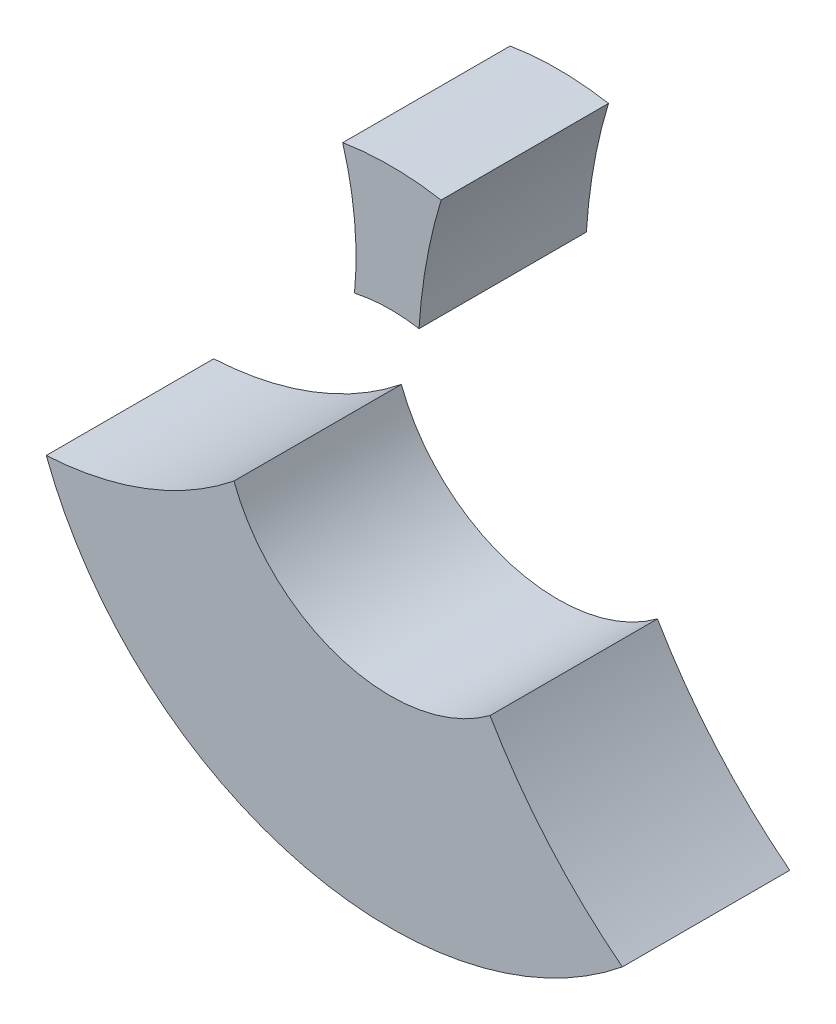
SolidWorks part; units mm, degrees
ref_plane "Front Plane" through (0, 0, 0) normal (0, 0, 1) x (1, 0, 0)
ref_plane "Top Plane" through (0, 0, 0) normal (0, 1, 0) x (1, 0, 0)
ref_plane "Right Plane" through (0, 0, 0) normal (1, 0, 0) x (0, 0, -1)
sketch "Sketch1" plane through (0, 0, 0) normal (0, 0, 1) x (1, 0, 0)
  circle A0 centre (0, 0) radius 6
  circle A1 centre (0, 0) radius 13.2
extrude "Boss-Extrude1" add sketch "Sketch1" along normal blind 6
sketch "Sketch2" plane through (0, 0, 6) normal (0, 0, 1) x (1, 0, 0)
  line L0 (0, 0) -> (0, 15.2) construction
  line L1 (-1.7101, 4.6985) -> (0, 0) construction
  line L2 (1.7101, 4.6985) -> (0, 0) construction
  arc A0 (-1.2309, 6.9809) -> (1.1223, 6.9992) centre (0, 0) cw
  arc A1 (-2.8199, 12.8953) -> (2.8199, 12.8953) centre (0, 0) cw
  arc A2 (-1.7101, 10.32) -> (1.8166, 10.3018) centre (0, 0) cw
  arc A3 (-2.8199, 12.8953) -> (-1.7101, 10.32) centre (-12.9505, 7.003) ccw
  arc A4 (2.8199, 12.8953) -> (1.8166, 10.3018) centre (20.0229, 4.7501) cw
extrude "Cut-Extrude1" cut sketch "Sketch2" against normal through all contours A1 A4 A2 A3
